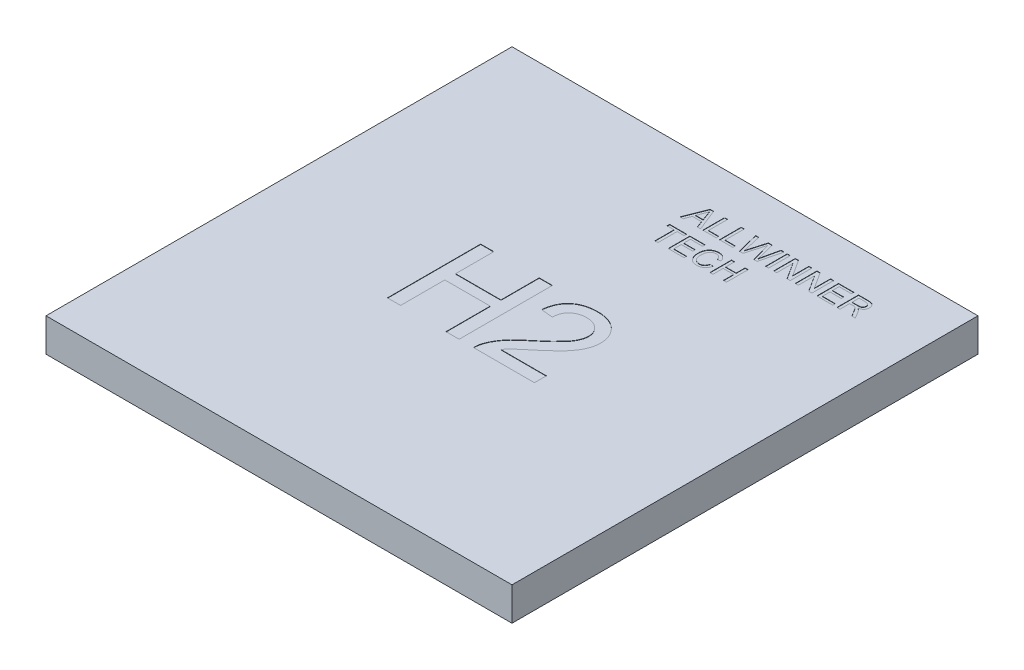
SolidWorks part; units mm, degrees
ref_plane "Спереди" through (0, 0, 0) normal (0, 0, 1) x (1, 0, 0)
ref_plane "Сверху" through (0, 0, 0) normal (0, 1, 0) x (1, 0, 0)
ref_plane "Справа" through (0, 0, 0) normal (1, 0, 0) x (0, 0, -1)
sketch "Эскиз1" plane through (0, 0, 0) normal (0, 1, 0) x (1, 0, 0)
  line L1 (7, -7) -> (-7, -7)
  line L2 (7, -7) -> (7, 7)
  line L3 (7, 7) -> (-7, 7)
  line L4 (-7, -7) -> (-7, 7)
  line L5 (7, -7) -> (-7, 7) construction
  line L6 (7, 7) -> (-7, -7) construction
  point P0 (0, 0)
  dimension "D1" = 14
  dimension "D2" = 14
extrude "Бобышка-Вытянуть1" add sketch "Эскиз1" along normal blind 1
sketch "Эскиз2" plane through (0, 1, 0) normal (0, 1, 0) x (1, 0, 0)
  text T0 "ALLWINNER\r\nTECH" font "Arial" height 0.65
  text T1 "H2" font "Arial" height 2.8
extrude "Вырез-Вытянуть1" cut sketch "Эскиз2" against normal blind 0.01
